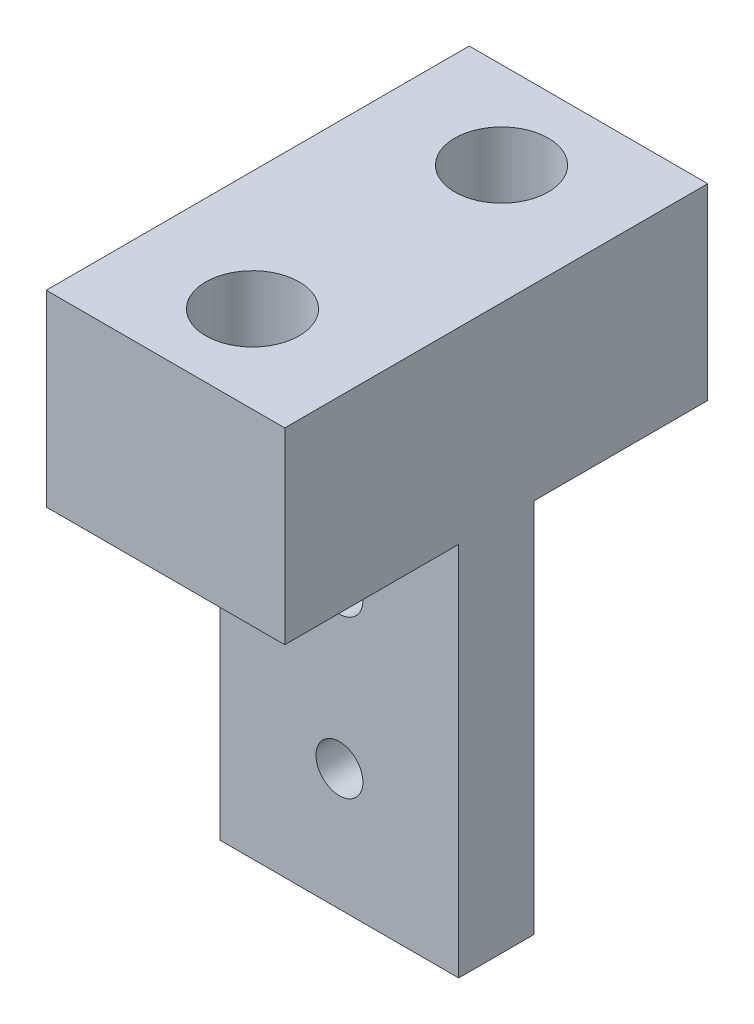
SolidWorks part; units mm, degrees
ref_plane "Plano frontal" through (0, 0, 0) normal (0, 0, 1) x (1, 0, 0)
ref_plane "Plano superior" through (0, 0, 0) normal (0, 1, 0) x (1, 0, 0)
ref_plane "Plano direito" through (0, 0, 0) normal (1, 0, 0) x (0, 0, -1)
ref_plane "Plano1" through (0, 0, 0) normal (-1, 0, 0) x (0, -1, 0)
sketch "Esboço1" plane through (0, 0, 0) normal (-1, 0, 0) x (0, -1, 0)
  line L0 (0, 0) -> (30, 0)
  line L1 (30, 0) -> (30, 22.5248)
  line L2 (30, 22.5248) -> (0, 22.5248)
  line L3 (0, 22.5248) -> (0, 0)
extrude "Ressalto-extrusão1" add sketch "Esboço1" against normal blind 12.7
sketch "Esboço2" plane through (12.7, 0, 0) normal (1, 0, 0) x (0, 0, -1)
  line L0 (0, -10) -> (-9.2624, -10)
  line L1 (-9.2624, -10) -> (-9.2624, -30)
  line L2 (-9.2624, -30) -> (0, -30)
  line L3 (0, -30) -> (0, -10)
extrude "Corte-extrusão1" cut sketch "Esboço2" against normal through all
sketch "Esboço3" plane through (12.7, 0, 0) normal (1, 0, 0) x (0, 0, -1)
  line L0 (-13.2624, -10) -> (-22.5248, -10)
  line L1 (-22.5248, -10) -> (-22.5248, -30)
  line L2 (-22.5248, -30) -> (-13.2624, -30)
  line L3 (-13.2624, -30) -> (-13.2624, -10)
extrude "Corte-extrusão2" cut sketch "Esboço3" against normal through all
hole_wizard "Furo1" positions "Esboço7" profile "Esboço6" legacy
sketch "Esboço7" plane through (0, -10, 0) normal (0, -1, 0) x (-1, 0, 0)
  point P0 (-6.35, -4.6312)
  point P1 (-6.35, -17.8936)
sketch "Esboço6" plane through (6.35, -10, 4.6312) normal (1, 0, 0) x (0, 0, -1)
  line L0 (0, 0) -> (0, 10)
  line L1 (0, 10) -> (2.4892, 10)
  line L2 (2.4892, 10) -> (2.4892, 4.1656)
  line L3 (2.4892, 4.1656) -> (3.9688, 4.1656)
  line L4 (3.9688, 4.1656) -> (3.9688, 0)
  line L5 (3.9688, 0) -> (0, 0)
  line L6 (0, 110) -> (0, -10) construction
  dimension "Diameter" = 4.9784
  dimension "Depth" = 10
  dimension "C-Bore Diameter" = 7.9375
  dimension "C-Bore Depth" = 4.1656
sketch "Esboço8" plane through (0, 0, 13.2624) normal (0, 0, 1) x (1, 0, 0)
  circle A0 centre (6.35, -15.1437) radius 1.25
  circle A1 centre (6.35, -23.5206) radius 1.25
extrude "Corte-extrusão3" cut sketch "Esboço8" against normal blind 10
